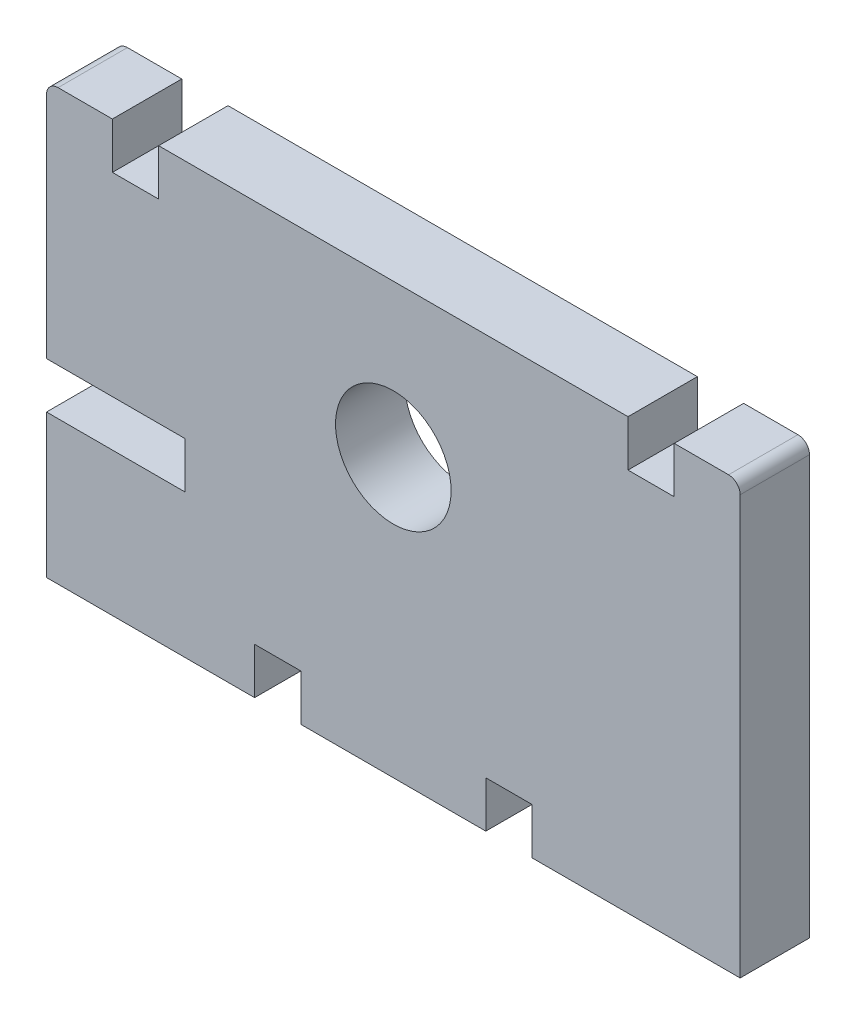
SolidWorks part; units mm, degrees
material "ﾊﾞﾙｻ"
ref_plane "正面" through (0, 0, 0) normal (0, 0, 1) x (1, 0, 0)
ref_plane "平面" through (0, 0, 0) normal (0, 1, 0) x (1, 0, 0)
ref_plane "右側面" through (0, 0, 0) normal (1, 0, 0) x (0, 0, -1)
sketch "ｽｹｯﾁ1" plane through (0, 0, 0) normal (0, 0, 1) x (1, 0, 0)
  line L1 (-15, 12) -> (15, 12)
  line L2 (-15, 12) -> (-15, -3.8)
  line L3 (-15, -12) -> (15, -12)
  line L4 (15, 12) -> (15, -12)
  line L5 (-15, 12) -> (15, -12) construction
  line L6 (-15, -12) -> (15, 12) construction
  line L9 (-15, -5.8) -> (-15, -12)
  line L10 (-15, -3.8) -> (-15, -5.8) construction
  line L11 (-15, -3.8) -> (-15, -5.8)
  line L12 (-15, 6.6) -> (15, 6.6)
  line L13 (-12.15, 6.6) -> (-12.15, 4.6)
  line L14 (-12.15, 4.6) -> (-10.15, 4.6)
  line L15 (-15, -5.8) -> (-9, -5.8)
  line L16 (-9, -5.8) -> (-9, -3.8)
  line L17 (-9, -3.8) -> (-15, -3.8)
  line L18 (-10.15, 4.6) -> (-10.15, 6.6)
  line L19 (0, 0) -> (0, -12) construction
  line L20 (12.15, 4.6) -> (10.15, 4.6)
  line L21 (12.15, 6.6) -> (12.15, 4.6)
  line L22 (10.15, 4.6) -> (10.15, 6.6)
  line L23 (-6, -12) -> (-6, -10)
  line L24 (-6, -10) -> (-4, -10)
  line L25 (-4, -10) -> (-4, -12)
  line L26 (6, -12) -> (6, -10)
  line L27 (6, -10) -> (4, -10)
  line L28 (4, -10) -> (4, -12)
  circle A0 centre (0, 0) radius 2.5
  dimension "D1" = 5
  dimension "D2" = 30
  dimension "D3" = 24
  dimension "D4" = 18.6
  dimension "D5" = 2
  dimension "D6" = 2
  dimension "D7" = 6.2
  dimension "D8" = 6
  dimension "D9" = 2
  dimension "D10" = 2.85
  dimension "D11" = 9
  dimension "D12" = 2
  dimension "D13" = 2
extrude "ﾎﾞｽ - 押し出し1" add sketch "ｽｹｯﾁ1" along normal blind 3
fillet "ﾌｨﾚｯﾄ1" radius 0.5 2 edges at (-15, 6.6, 1.5) (15, 6.6, 1.5)
